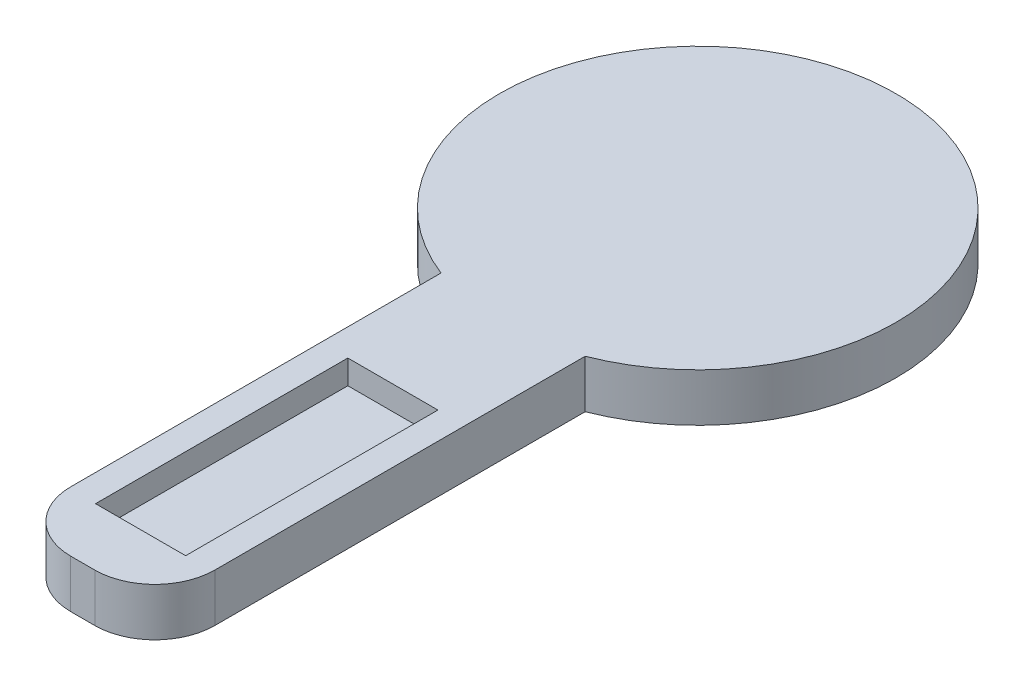
SolidWorks part; units mm, degrees
ref_plane "Front Plane" through (0, 0, 0) normal (0, 0, 1) x (1, 0, 0)
ref_plane "Top Plane" through (0, 0, 0) normal (0, 1, 0) x (1, 0, 0)
ref_plane "Right Plane" through (0, 0, 0) normal (1, 0, 0) x (0, 0, -1)
sketch "Sketch1" plane through (0, 0, 0) normal (0, 1, 0) x (1, 0, 0)
  line L0 (0, 93.9283) -> (0, -81.1352) construction
  line L3 (-6, 30) -> (6, 30)
  line L4 (-6, 30) -> (-6, -30)
  line L5 (-6, -30) -> (6, -30)
  line L6 (6, 30) -> (6, -30)
  line L7 (-64.9755, 0) -> (70.6987, 0) construction
  dimension "D2" = 60
  dimension "D1" = 12
extrude "Boss-Extrude1" add sketch "Sketch1" along normal blind 4
sketch "Sketch2" plane through (0, 4, 0) normal (0, 1, 0) x (1, 0, 0)
  line L0 (-13.6791, 21.185) -> (20.5769, 21.185) construction
  line L1 (-1.7496, 24.0066) -> (1.7496, 24.0066) construction
  line L2 (-1.7496, 24.0066) -> (-1.7496, 18.3634) construction
  line L3 (-1.7496, 18.3634) -> (1.7496, 18.3634) construction
  line L4 (1.7496, 24.0066) -> (1.7496, 18.3634) construction
  line L5 (-3.75, -4.185) -> (3.75, -4.185)
  line L6 (-3.75, -4.185) -> (-3.75, -25.185)
  line L7 (-3.75, -25.185) -> (3.75, -25.185)
  line L8 (3.75, -4.185) -> (3.75, -25.185)
  line L9 (-8.165, -21.185) -> (28.578, -21.185) construction
  line L10 (-24.9724, 0) -> (40.7727, 0) construction
  line L11 (0, 33.6512) -> (0, -35.6142) construction
  line L13 (-6, -30) -> (6, -30) construction
  circle A0 centre (0, -21.185) radius 3.5 construction
  dimension "D5" = 7
  dimension "D6" = 0.5
  dimension "D1" = 42.37
  dimension "D2" = 21.185
  dimension "D3" = 7.5
  dimension "D4" = 21
  dimension "D7" = 8.815
extrude "Cut-Extrude1" cut sketch "Sketch2" against normal blind 2
sketch "Sketch4" plane through (0, 0, 0) normal (0, -1, 0) x (1, 0, 0)
  line L1 (0, 0) -> (0, 36.451) construction
  line L2 (-6, 30) -> (6, 30) construction
  circle A0 centre (0, 21.18) radius 3.5
  dimension "D1" = 7
  dimension "D2" = 8.82
extrude "Boss-Extrude2" add sketch "Sketch4" along normal blind 1
sketch "Sketch5" plane through (0, 4, 0) normal (0, 1, 0) x (1, 0, 0)
  line L0 (0, 0) -> (0, 39.3701) construction
  circle A0 centre (0, 21.19) radius 16.5
  dimension "D2" = 33
  dimension "D1" = 21.19
extrude "Boss-Extrude3" add sketch "Sketch5" against normal blind 4
fillet "Fillet2" radius 5 2 edges at (6, 2, 30) (-6, 2, 30)
